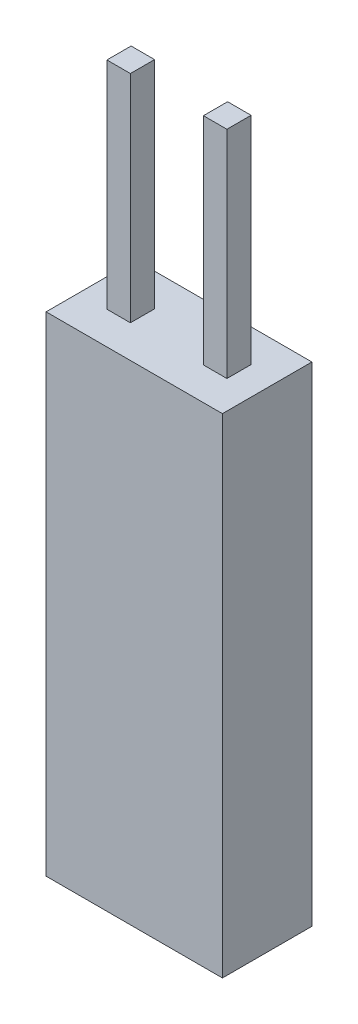
SolidWorks part; units mm, degrees
ref_plane "Front Plane" through (0, 0, 0) normal (0, 0, 1) x (1, 0, 0)
ref_plane "Top Plane" through (0, 0, 0) normal (0, 1, 0) x (1, 0, 0)
ref_plane "Right Plane" through (0, 0, 0) normal (1, 0, 0) x (0, 0, -1)
sketch "Sketch1" plane through (0, 0, 0) normal (0, 1, 0) x (1, 0, 0)
  line L1 (2.5527, 1.2954) -> (-2.5527, 1.2954)
  line L2 (2.5527, 1.2954) -> (2.5527, -1.2954)
  line L3 (2.5527, -1.2954) -> (-2.5527, -1.2954)
  line L4 (-2.5527, 1.2954) -> (-2.5527, -1.2954)
  line L5 (0, -1.2954) -> (0, 1.2954) construction
  line L6 (2.5527, 0) -> (-2.5527, 0) construction
  point P0 (0, 0)
  dimension "D1" = 5.1054
  dimension "D2" = 2.5908
extrude "Boss-Extrude1" add sketch "Sketch1" against normal blind 14.15
sketch "Sketch2" plane through (0, 0, 0) normal (0, 1, 0) x (1, 0, 0)
  line L0 (0, 1.2954) -> (0, 0) construction
  line L1 (-1.737, -0.35) -> (-1.057, -0.35)
  line L2 (-1.737, -0.35) -> (-1.737, 0.35)
  line L3 (-1.737, 0.35) -> (-1.057, 0.35)
  line L4 (-1.057, -0.35) -> (-1.057, 0.35)
  line L5 (-1.397, 0.35) -> (-1.397, -0.35) construction
  line L6 (-1.737, 0) -> (-1.057, 0) construction
  line L7 (2.5527, 1.2954) -> (-2.5527, 1.2954) construction
  line L8 (1.057, 0) -> (-1.057, 0) construction
  line L9 (1.737, 0) -> (1.057, 0) construction
  line L10 (1.397, 0.35) -> (1.397, -0.35) construction
  line L11 (1.057, -0.35) -> (1.057, 0.35)
  line L12 (1.737, 0.35) -> (1.057, 0.35)
  line L13 (1.737, -0.35) -> (1.737, 0.35)
  line L14 (1.737, -0.35) -> (1.057, -0.35)
  point P0 (-1.397, 0)
  point P16 (1.397, 0)
  dimension "D1" = 0.7
  dimension "D2" = 0.68
  dimension "D3" = 2.794
extrude "Boss-Extrude2" add sketch "Sketch2" along normal blind 6.25
